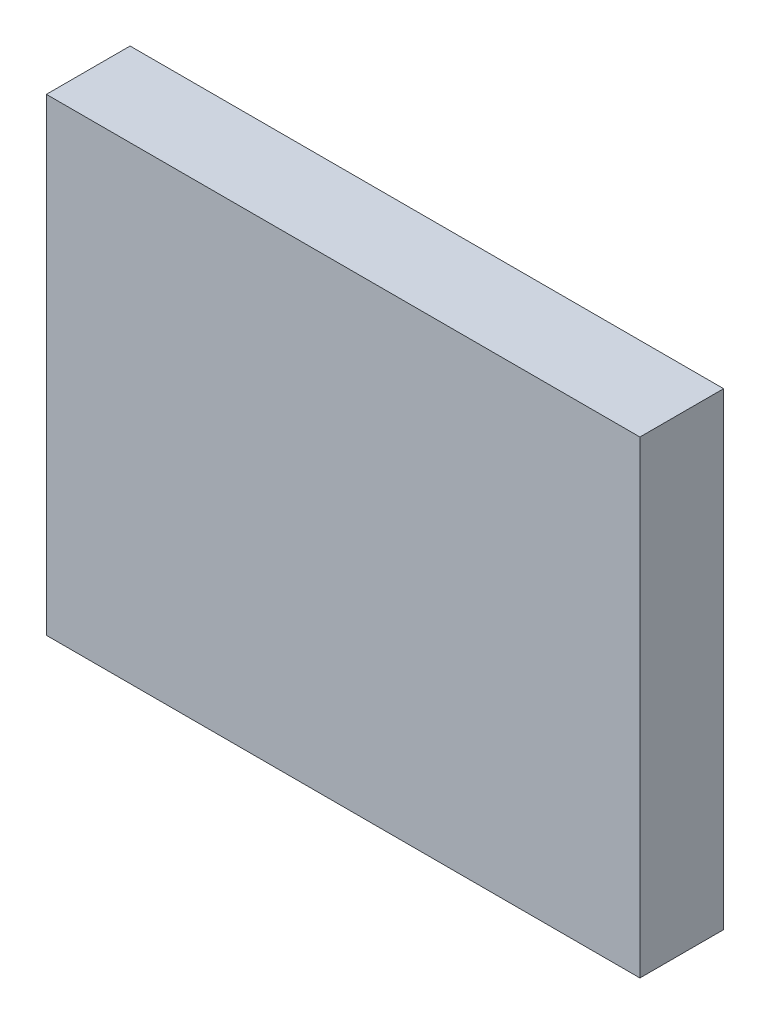
SolidWorks part; units mm, degrees
ref_plane "Ebene vorne" through (0, 0, 0) normal (0, 0, 1) x (1, 0, 0)
ref_plane "Ebene oben" through (0, 0, 0) normal (0, 1, 0) x (1, 0, 0)
ref_plane "Ebene rechts" through (0, 0, 0) normal (1, 0, 0) x (0, 0, -1)
sketch "Skizze1" plane through (0, 0, 0) normal (0, 0, 1) x (1, 0, 0)
  line L1 (-70.9053, 55.9708) -> (0, 55.9708)
  line L2 (-70.9053, 55.9708) -> (-70.9053, 0)
  line L3 (-70.9053, 0) -> (0, 0)
  line L4 (0, 55.9708) -> (0, 0)
extrude "Aufsatz-Linear austragen1" add sketch "Skizze1" along normal blind 10
other "Einfrieren***"
